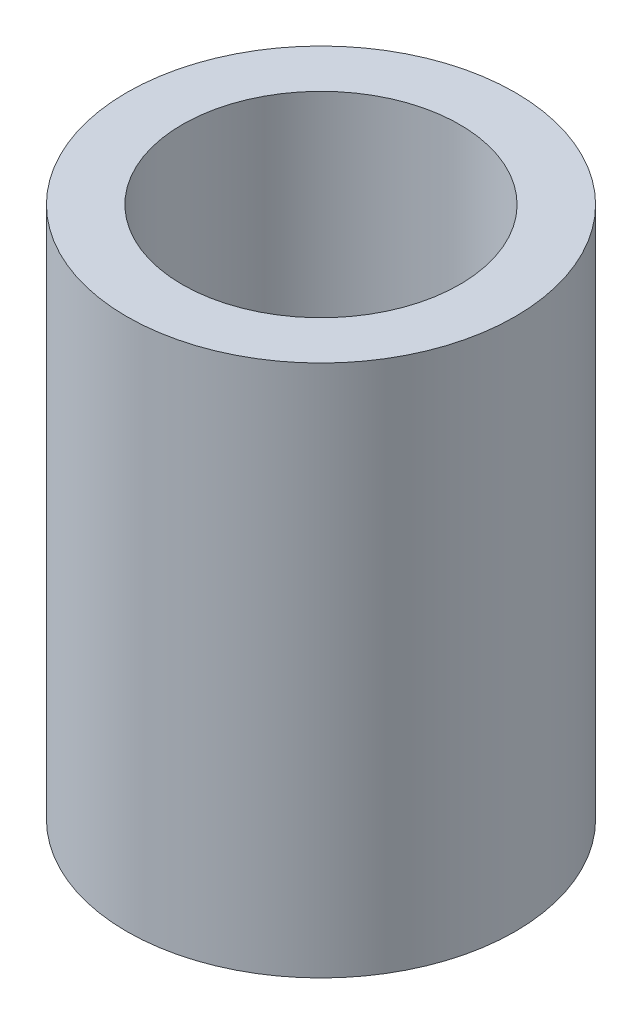
SolidWorks part; units mm, degrees
ref_plane "Front Plane" through (0, 0, 0) normal (0, 0, 1) x (1, 0, 0)
ref_plane "Top Plane" through (0, 0, 0) normal (0, 1, 0) x (1, 0, 0)
ref_plane "Right Plane" through (0, 0, 0) normal (1, 0, 0) x (0, 0, -1)
sketch "Sketch1" plane through (0, 0, 0) normal (0, 1, 0) x (1, 0, 0)
  circle A0 centre (0, 0) radius 3.5
  circle A1 centre (0, 0) radius 2.5
  dimension "D1" = 5
  dimension "D2" = 7
extrude "Boss-Extrude1" add sketch "Sketch1" along normal blind 9.6
